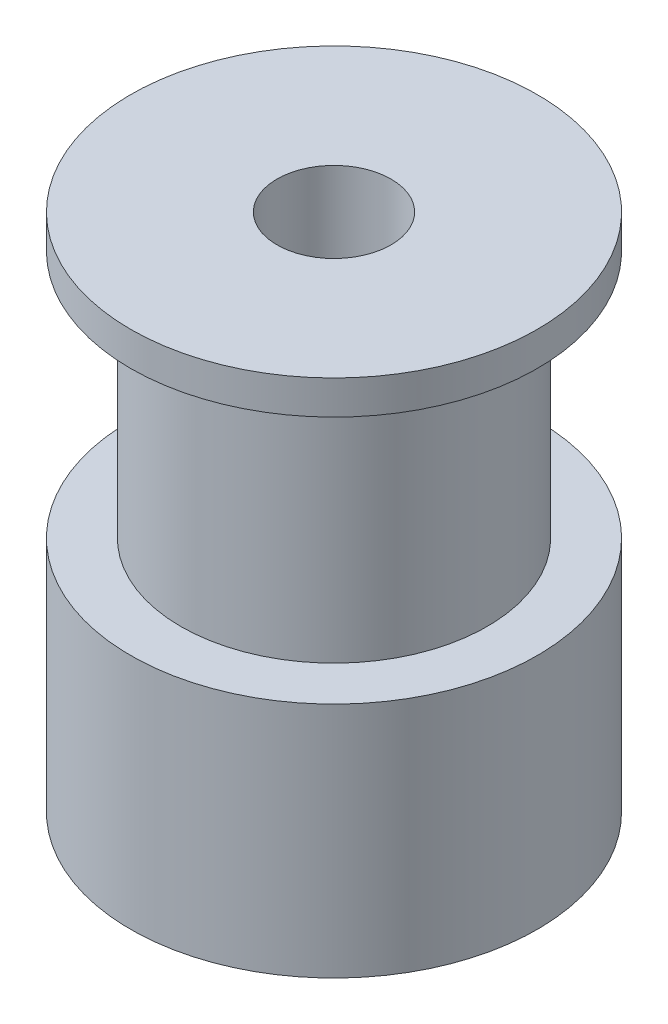
SolidWorks part; units mm, degrees
ref_plane "前视基准面" through (0, 0, 0) normal (0, 0, 1) x (1, 0, 0)
ref_plane "上视基准面" through (0, 0, 0) normal (0, 1, 0) x (1, 0, 0)
ref_plane "右视基准面" through (0, 0, 0) normal (1, 0, 0) x (0, 0, -1)
sketch "草图1" plane through (0, 0, 0) normal (0, 1, 0) x (1, 0, 0)
  circle A0 centre (0, 0) radius 6.78
  dimension "D1" = 13.56
extrude "凸台-拉伸2" add sketch "草图1" along normal blind 11
sketch "草图3" plane through (0, 11, 0) normal (0, 1, 0) x (1, 0, 0)
  circle A0 centre (0, 0) radius 9
  dimension "D1" = 18
extrude "凸台-上挡边" add sketch "草图3" along normal blind 1.5
sketch "草图4" plane through (0, 0, 0) normal (0, -1, 0) x (1, 0, 0)
  circle A0 centre (0, 0) radius 9
  dimension "D1" = 18
extrude "凸台-下挡边" add sketch "草图4" along normal blind 10.5
sketch "草图5" plane through (0, -10.5, 0) normal (0, -1, 0) x (1, 0, 0)
  circle A0 centre (0, 0) radius 2.525
  dimension "D1" = 5.05
extrude "切除-轴孔" cut sketch "草图5" against normal through all
